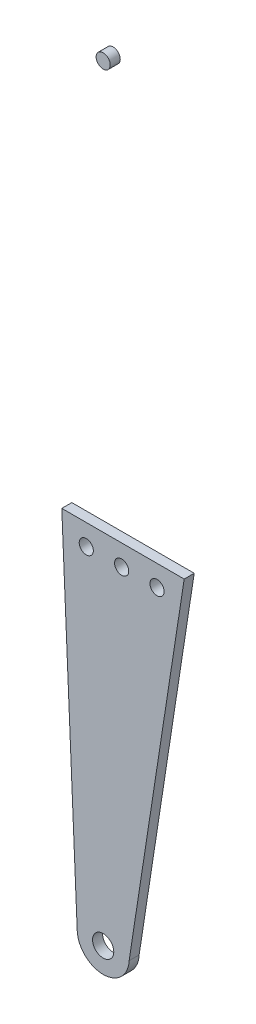
SolidWorks part; units mm, degrees
ref_plane "Front Plane" through (0, 0, 0) normal (0, 0, 1) x (1, 0, 0)
ref_plane "Top Plane" through (0, 0, 0) normal (0, 1, 0) x (1, 0, 0)
ref_plane "Right Plane" through (0, 0, 0) normal (1, 0, 0) x (0, 0, -1)
sketch "Sketch1" plane through (0, 0, 0) normal (0, 0, 1) x (1, 0, 0)
  line L0 (58.9105, 262.9177) -> (58.9105, -62.0823) construction
  line L1 (41.3586, 89.8031) -> (47.9105, -62.0823)
  line L2 (36.9105, 192.9177) -> (42.087, 72.9177) construction
  line L3 (47.9105, -62.0823) -> (58.9105, -62.0823) construction
  line L4 (58.9105, -62.0823) -> (69.9105, -62.0823) construction
  line L5 (93.2727, 89.8031) -> (69.9105, -62.0823)
  line L6 (90.6755, 72.9177) -> (105.7494, 170.9177) construction
  line L7 (41.3586, 89.8031) -> (93.2727, 89.8031)
  circle A0 centre (58.9105, -62.0823) radius 4.5
  circle A1 centre (58.9105, 262.9177) radius 3 construction
  circle A2 centre (58.9105, 262.9177) radius 3
  arc A3 (47.9105, -62.0823) -> (69.9105, -62.0823) centre (58.9105, -61.6078) ccw
  dimension "D1" = 9
  dimension "D2" = 325
  dimension "D3" = 151.8854
  dimension "D4" = 11
extrude "Boss-Extrude1" add sketch "Sketch1" along normal up to surface (4.25 mm away) contours L5 A3 L1 L7
sketch "Sketch2" plane through (0, 0, 4.25) normal (0, 0, 1) x (1, 0, 0)
  circle A0 centre (51.7512, 80.9177) radius 3
  circle A1 centre (66.7512, 80.9177) radius 3
  circle A2 centre (81.7512, 80.9177) radius 3
  dimension "D1" = 6
  dimension "D2" = 6
  dimension "D3" = 6
extrude "Cut-Extrude1" cut sketch "Sketch2" against normal blind 10
